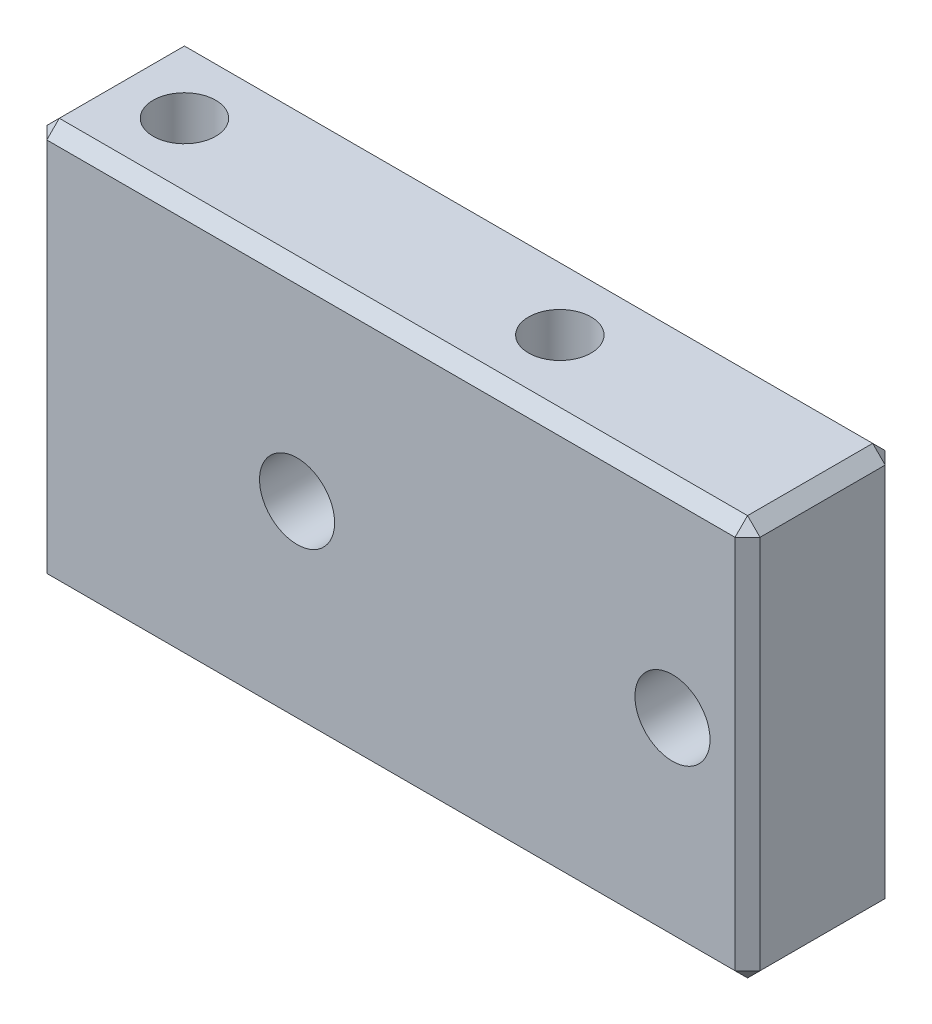
SolidWorks part; units mm, degrees
material "6061 合金"
ref_plane "前视基准面" through (0, 0, 0) normal (0, 0, 1) x (1, 0, 0)
ref_plane "上视基准面" through (0, 0, 0) normal (0, 1, 0) x (1, 0, 0)
ref_plane "右视基准面" through (0, 0, 0) normal (1, 0, 0) x (0, 0, -1)
sketch "草图2" plane through (0, 0, 0) normal (0, 0, 1) x (1, 0, 0)
  line L10 (3, 8) -> (3, -8)
  line L11 (0, 0) -> (-15, 0) construction
  line L41 (3, -8) -> (-25.5, -8)
  line L48 (-25.5, 8) -> (3, 8)
  line L49 (-25.5, 8) -> (-25.5, -8)
  circle A3 centre (-15, 0) radius 1.5
  circle A5 centre (0, 0) radius 1.5
  dimension "D1" = 15
  dimension "D2" = 3
  dimension "D3" = 8
  dimension "D4" = 10.5
  dimension "D7" = 3
  dimension "D6" = 8
extrude "凸台-拉伸1" add sketch "草图2" along normal mid plane 6
hole_wizard "M3 螺纹孔1" [suppressed] positions "草图5" profile "草图4" tap size "M3" standard "GB"
sketch "草图5" plane through (0, 0, 3) normal (0, 0, 1) x (1, 0, 0)
  point P0 (0, 0)
  point P3 (-15, 0)
sketch "草图4" plane through (0, 0, 3) normal (1, 0, 0) x (0, -1, 0)
  line L0 (0, 0) -> (0, 6)
  line L1 (0, 6) -> (1.25, 6)
  line L2 (1.25, 6) -> (1.25, 0)
  line L5 (1.25, 0) -> (0, 0)
  line L11 (0, -6.35) -> (0, 107.95) construction
  dimension "通孔螺纹孔钻头直径" = 2.5
  dimension "通孔螺纹孔钻头深度" = 6
hole_wizard "M3 螺纹孔2" positions "草图6" profile "草图7" tap size "M3" standard "GB" end condition through all
sketch "草图6" plane through (0, 8, 0) normal (0, 1, 0) x (1, 0, 0)
  line L1 (-22.5, 0) -> (0, 0) construction
  line L2 (-25.5, -3) -> (-25.5, 3) construction
  point P0 (-7.5, 0)
  point P2 (-22.5, 0)
  dimension "D1" = 3
  dimension "D2" = 15
sketch "草图7" plane through (-7.5, 8, 0) normal (1, 0, 0) x (0, 0, 1)
  line L0 (0, 0) -> (0, 16)
  line L1 (0, 16) -> (1.25, 16)
  line L2 (1.25, 16) -> (1.25, 0)
  line L5 (1.25, 0) -> (0, 0)
  line L11 (0, -6.35) -> (0, 107.95) construction
  dimension "通孔螺纹孔钻头直径" = 2.5
  dimension "通孔螺纹孔钻头深度" = 16
cosmetic thread "孔螺蚊线5" parameters "D2"=3
cosmetic thread "孔螺蚊线6" parameters "D2"=3
chamfer "倒角1" distance 0.5 angle 45 12 edges at (-11.25, -8, -3) (-11.25, -8, 3) (-25.5, 0, -3) (-25.5, 0, 3) (3, -8, 0) (3, 0, 3) (3, 0, -3) (-11.25, 8, -3) (3, 8, 0) (-11.25, 8, 3) (-25.5, 8, 0) (-25.5, -8, 0)
